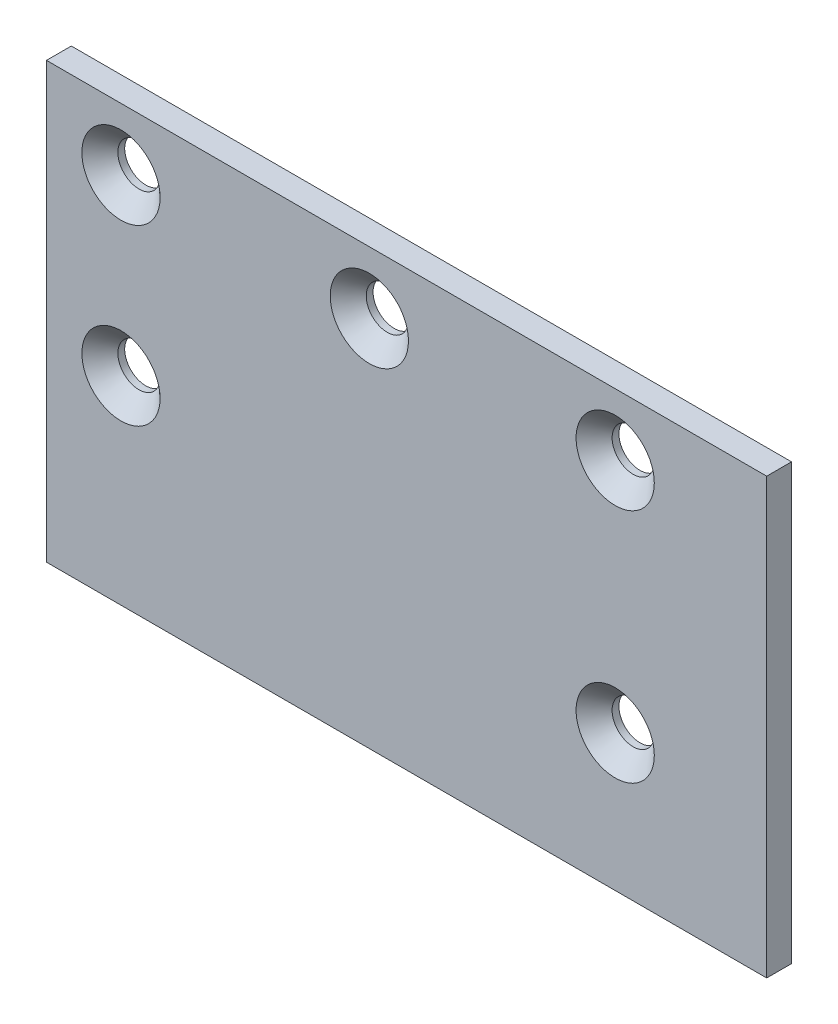
SolidWorks part; units mm, degrees
ref_plane "Front Plane" through (0, 0, 0) normal (0, 0, 1) x (1, 0, 0)
ref_plane "Top Plane" through (0, 0, 0) normal (0, 1, 0) x (1, 0, 0)
ref_plane "Right Plane" through (0, 0, 0) normal (1, 0, 0) x (0, 0, -1)
sketch "Sketch1" plane through (0, 0, 0) normal (0, 0, 1) x (1, 0, 0)
  line L1 (-29, 17.5) -> (29, 17.5)
  line L2 (-29, 17.5) -> (-29, -17.5)
  line L3 (-29, -17.5) -> (29, -17.5)
  line L4 (29, 17.5) -> (29, -17.5)
  line L5 (-29, 17.5) -> (29, -17.5) construction
  line L6 (-29, -17.5) -> (29, 17.5) construction
  point P0 (0, 0)
  dimension "D1" = 58
  dimension "D2" = 35
extrude "Boss-Extrude1" add sketch "Sketch1" along normal blind 2
hole_wizard "CSK for M3 Flat Countersunk Head Screw1" positions "Sketch4" profile "Sketch3" countersink size "M3" standard "JIS" end condition through all
sketch "Sketch4" plane through (0, 0, 2) normal (0, 0, 1) x (1, 0, 0)
  line L1 (-29, -17.5) -> (29, -17.5) construction
  line L2 (29, -17.5) -> (29, 17.5) construction
  point P0 (-23, 12.5)
  point P2 (-3, 12.5)
  point P4 (16.8, 12.5)
  point P6 (16.8, -6.5)
  point P8 (-23, -1.5)
  point P16 (21.12, -6.0686)
  point P21 (20.5792, 9.7939)
  point P26 (0, 0)
  point P27 (0, 0)
  point P28 (0, 0)
  point P29 (0, 0)
  dimension "D1" = 11
  dimension "D2" = 19
  dimension "D3" = 12.2
  dimension "D4" = 19.8
  dimension "D5" = 20
  dimension "D6" = 16
sketch "Sketch3" plane through (-23, 12.5, 2) normal (1, 0, 0) x (0, -1, 0)
  line L0 (0, 0) -> (0, 2)
  line L1 (0, 2) -> (1.7, 2)
  line L2 (1.7, 2) -> (1.7, 1.45)
  line L3 (1.7, 1.45) -> (3.15, 0)
  line L5 (3.15, 0) -> (0, 0)
  line L6 (-1.7, 1.45) -> (-3.15, 0) construction
  line L11 (0, -6.35) -> (0, 107.95) construction
  dimension "Thru Hole Dia." = 3.4
  dimension "Thru Hole Depth" = 2
  dimension "Near C'Sink Dia." = 6.3
  dimension "Near C'Sink Angle" = 90
